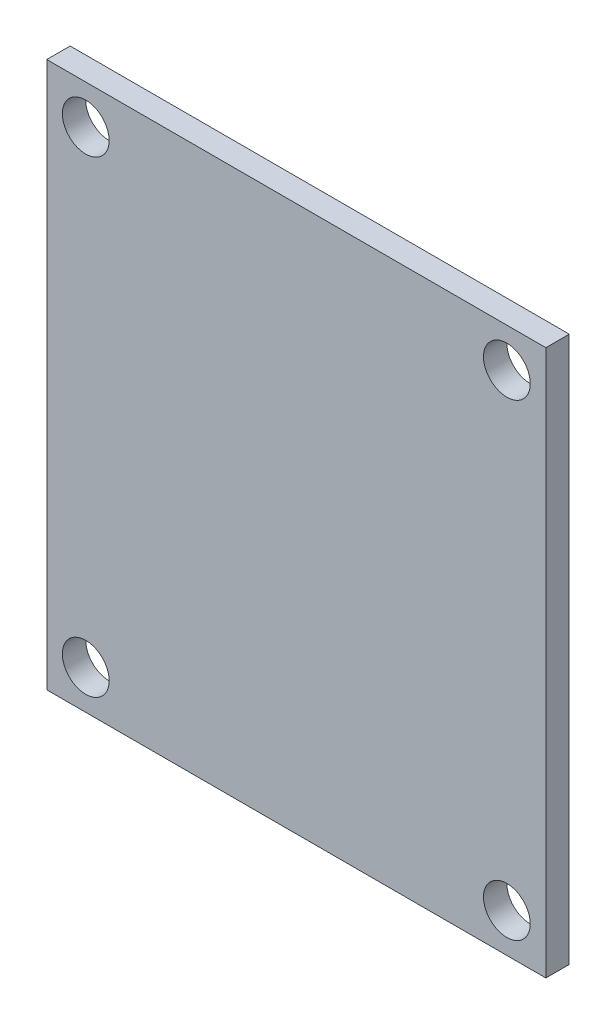
SolidWorks part; units mm, degrees
ref_plane "Спереди" through (0, 0, 0) normal (0, 0, 1) x (1, 0, 0)
ref_plane "Сверху" through (0, 0, 0) normal (0, 1, 0) x (1, 0, 0)
ref_plane "Справа" through (0, 0, 0) normal (1, 0, 0) x (0, 0, -1)
other "Configuration Table"
sketch "Эскиз1" plane through (0, 0, 0) normal (0, 0, 1) x (1, 0, 0)
  line L0 (0, 17.5) -> (32, 17.5) construction
  line L1 (0, 0) -> (32, 0)
  line L2 (0, 0) -> (0, 35)
  line L3 (0, 35) -> (32, 35)
  line L4 (32, 0) -> (32, 35)
  line L5 (16, 35) -> (16, 0) construction
  circle A0 centre (2.5, 32.5) radius 1.5
  circle A1 centre (29.5, 32.5) radius 1.5
  circle A2 centre (29.5, 2.5) radius 1.5
  circle A3 centre (2.5, 2.5) radius 1.5
  point P11 (0, 0)
  dimension "D5" = 3
  dimension "D1" = 35
  dimension "D2" = 32
  dimension "D3" = 2.5
  dimension "D4" = 2.5
extrude "Бобышка-Вытянуть1" add sketch "Эскиз1" along normal blind 1.5
